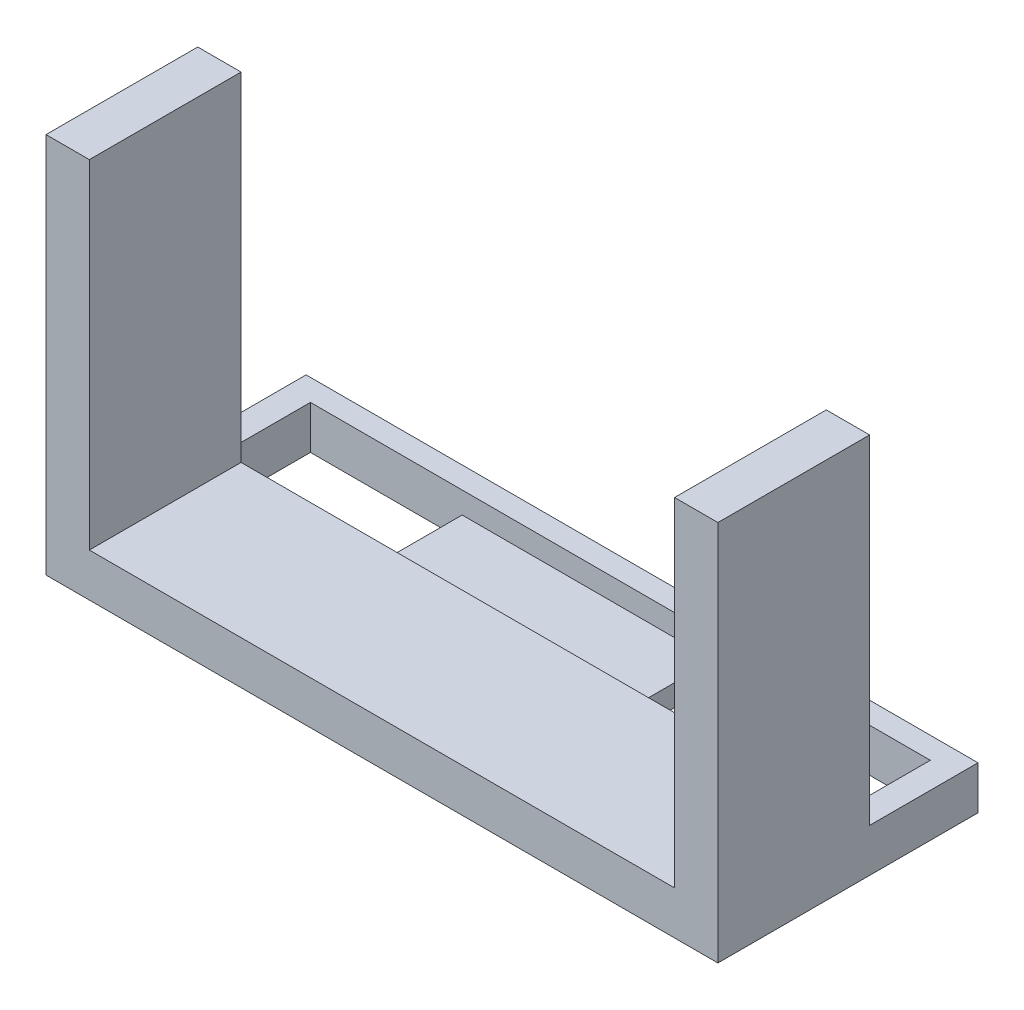
SolidWorks part; units mm, degrees
ref_plane "Front Plane" through (0, 0, 0) normal (0, 0, 1) x (1, 0, 0)
ref_plane "Top Plane" through (0, 0, 0) normal (0, 1, 0) x (1, 0, 0)
ref_plane "Right Plane" through (0, 0, 0) normal (1, 0, 0) x (0, 0, -1)
sketch "Sketch1" plane through (0, 0, 0) normal (0, 1, 0) x (1, 0, 0)
  line L1 (0, 0) -> (155, 0)
  line L2 (0, 0) -> (0, -60)
  line L3 (0, -60) -> (155, -60)
  line L4 (155, 0) -> (155, -60)
  dimension "D1" = 155
  dimension "D2" = 60
extrude "Boss-Extrude1" add sketch "Sketch1" along normal blind 10
sketch "Sketch2" plane through (0, 10, 0) normal (0, 1, 0) x (1, 0, 0)
  line L0 (155, 0) -> (0, 0) construction
  line L1 (6, -5) -> (149, -5)
  line L2 (6, -5) -> (6, -25)
  line L3 (6, -25) -> (149, -25)
  line L4 (149, -5) -> (149, -25)
  line L5 (0, 0) -> (0, -60) construction
  line L6 (155, -60) -> (155, 0) construction
  dimension "D1" = 5
  dimension "D2" = 6
  dimension "D3" = 6
  dimension "D4" = 20
extrude "Cut-Extrude1" cut sketch "Sketch2" against normal blind 5
sketch "Sketch3" plane through (0, 10, 0) normal (0, 1, 0) x (1, 0, 0)
  line L0 (0, 0) -> (0, -60) construction
  line L1 (10, -25) -> (0, -25)
  line L2 (10, -25) -> (10, -60)
  line L3 (10, -60) -> (0, -60)
  line L4 (0, -25) -> (0, -60)
  line L5 (0, -60) -> (155, -60) construction
  line L6 (6, -25) -> (149, -25) construction
  line L7 (155, -60) -> (155, 0) construction
  line L8 (145, -25) -> (155, -25)
  line L9 (145, -25) -> (145, -60)
  line L10 (145, -60) -> (155, -60)
  line L11 (155, -25) -> (155, -60)
  line L12 (6, -25) -> (149, -25) construction
  dimension "D1" = 0
  dimension "D2" = 0
  dimension "D3" = 10
  dimension "D4" = 0
  dimension "D5" = 0
  dimension "D6" = 0
  dimension "D7" = 0
  dimension "D8" = 10
extrude "Boss-Extrude2" add sketch "Sketch3" along normal blind 78
sketch "Sketch4" plane through (0, 5, 0) normal (0, 1, 0) x (1, 0, 0)
  line L0 (6, -5) -> (6, -25) construction
  line L1 (6, -5) -> (41, -5)
  line L2 (6, -5) -> (6, -25)
  line L3 (6, -25) -> (41, -25)
  line L4 (41, -5) -> (41, -25)
  line L5 (99, -5) -> (149, -5)
  line L6 (99, -5) -> (99, -25)
  line L7 (99, -25) -> (149, -25)
  line L8 (149, -5) -> (149, -25)
  line L9 (149, -5) -> (6, -5) construction
  line L10 (6, -25) -> (149, -25) construction
  line L11 (149, -25) -> (149, -5) construction
  dimension "D1" = 0
  dimension "D2" = 0
  dimension "D3" = 0
  dimension "D4" = 35
  dimension "D5" = 0
  dimension "D6" = 0
  dimension "D7" = 0
  dimension "D8" = 50
extrude "Cut-Extrude2" cut sketch "Sketch4" against normal blind 78
